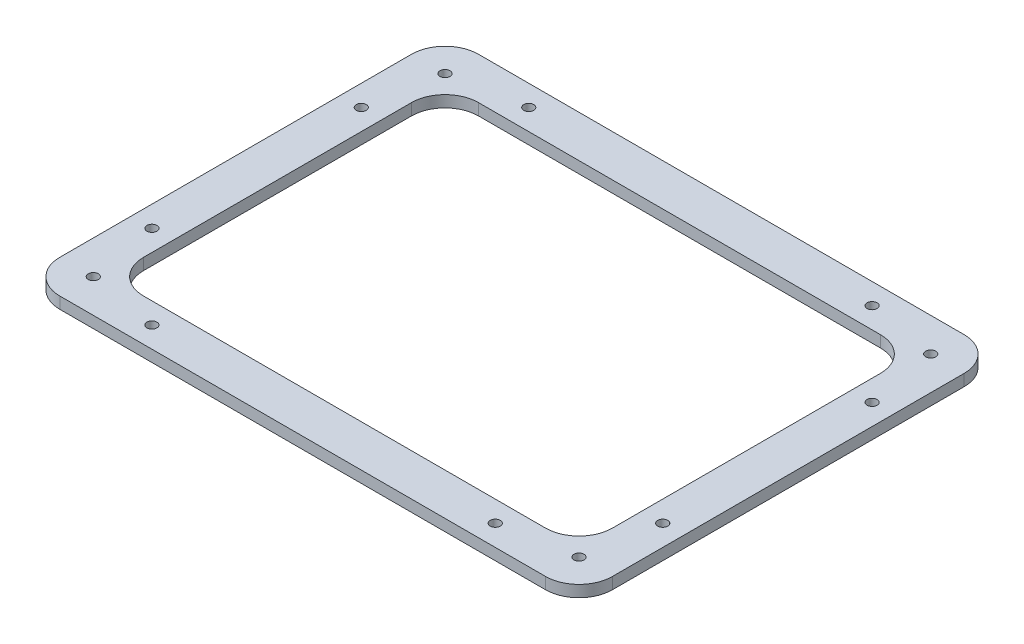
SolidWorks part; units mm, degrees
material "Delrin 2700 NC010, Low Viscosity Acetal Copolymer (SS)"
ref_plane "Front Plane" through (0, 0, 0) normal (0, 0, 1) x (1, 0, 0)
ref_plane "Top Plane" through (0, 0, 0) normal (0, 1, 0) x (1, 0, 0)
ref_plane "Right Plane" through (0, 0, 0) normal (1, 0, 0) x (0, 0, -1)
sketch "Sketch1" plane through (0, 0, 0) normal (0, 1, 0) x (1, 0, 0)
  line L0 (165, 125) -> (-165, -125) construction
  line L5 (-165, -125) -> (165, -125)
  line L6 (-165, -125) -> (-165, 125)
  line L7 (-165, 125) -> (165, 125)
  line L8 (165, -125) -> (165, 125)
  point P5 (0, 0)
  dimension "D1" = 330
  dimension "D2" = 250
extrude "Boss-Extrude1" add sketch "Sketch1" along normal blind 6.9
sketch "Sketch2" plane through (0, 6.9, 0) normal (0, 1, 0) x (1, 0, 0)
  line L0 (145, 105) -> (-145, -105) construction
  line L1 (-145, 105) -> (145, 105) construction
  line L2 (-145, 105) -> (-145, -105) construction
  line L3 (-145, -105) -> (145, -105) construction
  line L4 (145, 105) -> (145, -105) construction
  line L5 (0, 105) -> (0, 125) construction
  line L6 (165, 125) -> (-165, 125) construction
  line L8 (-145, 0) -> (-165, 0) construction
  line L9 (-165, 125) -> (-165, -125) construction
  circle A0 centre (-145, 105) radius 3
  circle A1 centre (145, 105) radius 3
  circle A2 centre (145, -105) radius 3
  circle A3 centre (-145, -105) radius 3
  point P4 (0, 0)
  dimension "D2" = 6
  dimension "D1" = 20
extrude "Cut-Extrude1" cut sketch "Sketch2" against normal through all
sketch "Sketch3" plane through (0, 6.9, 0) normal (0, 1, 0) x (1, 0, 0)
  line L0 (140, 100) -> (-140, -100) construction
  line L1 (-140, 100) -> (140, 100)
  line L2 (-140, 100) -> (-140, -100)
  line L3 (-140, -100) -> (140, -100)
  line L4 (140, 100) -> (140, -100)
  line L5 (0, 125) -> (0, 100) construction
  line L6 (165, 125) -> (-165, 125) construction
  line L8 (-140, 0) -> (-165, 0) construction
  line L9 (-165, 125) -> (-165, -125) construction
  point P4 (0, 0)
  dimension "D1" = 25
extrude "Cut-Extrude2" cut sketch "Sketch3" against normal through all
fillet "Fillet1" radius 20 4 edges at (165, 3.45, -125) (-165, 3.45, -125) (-165, 3.45, 125) (165, 3.45, 125)
fillet "Fillet2" radius 20 4 edges at (-140, 3.45, 100) (140, 3.45, 100) (140, 3.45, -100) (-140, 3.45, -100)
sketch "Sketch4" plane through (0, 6.9, 0) normal (0, 1, 0) x (1, 0, 0)
  line L0 (-152.5, -112.5) -> (-102.5, -112.5) construction
  line L1 (-102.5, -112.5) -> (-152.5, -62.5) construction
  line L2 (-152.5, -62.5) -> (-152.5, -112.5) construction
  line L3 (-152.5, -112.5) -> (-127.5, -87.5) construction
  line L4 (0, 100) -> (0, -100) construction
  line L5 (120, 100) -> (-120, 100) construction
  line L6 (-120, -100) -> (120, -100) construction
  line L7 (0, -100) -> (140, 0) construction
  line L8 (140, -80) -> (140, 80) construction
  line L9 (140, 0) -> (-140, 0) construction
  line L10 (-140, 80) -> (-140, -80) construction
  line L11 (-159.1421, -119.1421) -> (-152.5, -112.5) construction
  line L12 (-165, 105) -> (-165, -105) construction
  circle A0 centre (-152.5, -62.5) radius 3
  circle A1 centre (-102.5, -112.5) radius 3
  circle A2 centre (102.5, -112.5) radius 3
  circle A3 centre (152.5, -62.5) radius 3
  circle A4 centre (152.5, 62.5) radius 3
  circle A5 centre (102.5, 112.5) radius 3
  circle A6 centre (-102.5, 112.5) radius 3
  circle A7 centre (-152.5, 62.5) radius 3
  arc A9 (-165, -105) -> (-145, -125) centre (-145, -105) ccw construction
  point P38 (-130, -81.8894)
  point P39 (0, 0)
  point P40 (-159.1421, -119.1421)
  dimension "D2" = 6
  dimension "D1" = 50
  dimension "D3" = 12.5
extrude "Cut-Extrude3" cut sketch "Sketch4" against normal through all
